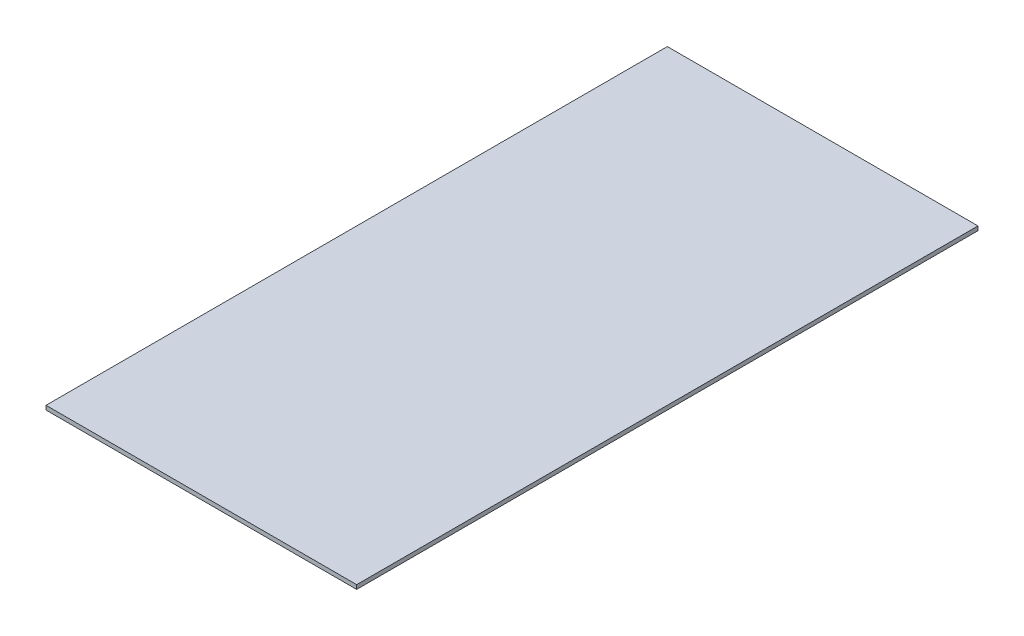
SolidWorks part; units mm, degrees
ref_plane "正面" through (0, 0, 0) normal (0, 0, 1) x (1, 0, 0)
ref_plane "平面" through (0, 0, 0) normal (0, 1, 0) x (1, 0, 0)
ref_plane "右側面" through (0, 0, 0) normal (1, 0, 0) x (0, 0, -1)
sketch "ｽｹｯﾁ1" plane through (0, 0, 0) normal (0, 0, 1) x (1, 0, 0)
  line L1 (-257.1429, 273.588) -> (642.8571, 273.588)
  line L2 (-257.1429, 273.588) -> (-257.1429, 261.588)
  line L3 (-257.1429, 261.588) -> (642.8571, 261.588)
  line L4 (642.8571, 273.588) -> (642.8571, 261.588)
  dimension "D1" = 900
  dimension "D2" = 12
extrude "ﾎﾞｽ - 押し出し1" add sketch "ｽｹｯﾁ1" along normal blind 1800
